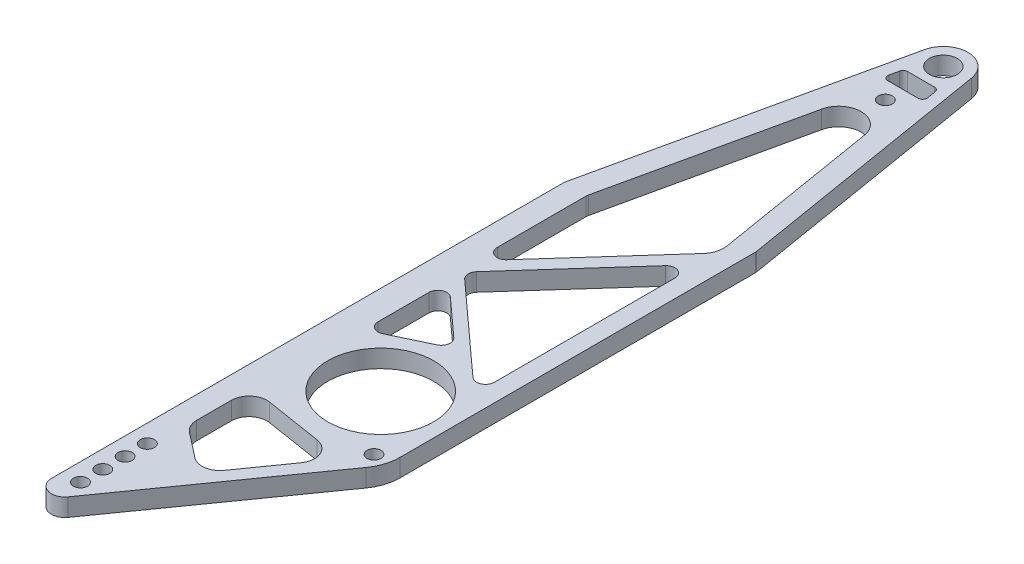
SolidWorks part; units mm, degrees
material "6061-T6 (SS)"
ref_plane "X-Y Datum" through (0, 0, 0) normal (0, 0, 1) x (1, 0, 0)
ref_plane "X-Z Datum" through (0, 0, 0) normal (0, 1, 0) x (1, 0, 0)
ref_plane "Y-Z Datum" through (0, 0, 0) normal (1, 0, 0) x (0, 0, -1)
other "Graphic1" [suppressed]
other "Graphic (Closed) -1" [suppressed]
sketch "Sketch1" plane through (0, 0, 0) normal (0, 1, 0) x (1, 0, 0)
  line L0 (25.4, -82.7357) -> (25.4, -202.7088)
  line L2 (-25.4, -229.1053) -> (-25.4, -131.2787)
  line L6 (25.4, -160.2465) -> (-25.4, -160.2465) construction
  line L28 (22.225, -208.2081) -> (-19.685, -232.4048)
  line L29 (0, 0) -> (41.91, 0) construction
  line L30 (41.91, 0) -> (0, -160.2465) construction
  line L31 (0, -160.2465) -> (0, 0) construction
  line L32 (-20.32, -219.075) -> (-20.32, -212.725) construction
  line L33 (25.2486, -81.3572) -> (6.8184, 1.5163)
  line L34 (-25.4, -131.2787) -> (-6.9178, 0.9668)
  circle A0 centre (0, 0) radius 3.9688
  circle A2 centre (0, -160.2465) radius 15.0813
  circle A6 centre (-20.32, -225.425) radius 2
  circle A7 centre (-20.32, -219.075) radius 2
  circle A8 centre (-20.32, -212.725) radius 2
  circle A9 centre (-20.32, -206.375) radius 2
  arc A10 (6.8184, 1.5163) -> (-6.9178, 0.9668) centre (0, 0) ccw
  circle A41 centre (0, -16.51) radius 2
  arc A42 (-25.4, -229.1053) -> (-19.685, -232.4048) centre (-21.59, -229.1053) ccw
  arc A43 (25.4, -202.7088) -> (22.225, -208.2081) centre (19.05, -202.7088) cw
  circle A45 centre (21.59, -82.0382) radius 2 construction
  arc A46 (25.2486, -81.3572) -> (25.4, -82.7357) centre (19.05, -82.7357) cw
  point P21 (-20.32, -215.9)
  point P30 (25.4, -206.375)
  point P51 (25.4, -82.0382)
  dimension "D1" = 7.9375
  dimension "D4" = 30.1625
  dimension "D8" = 4
  dimension "D6" = 6.985
  dimension "D65" = 4
  dimension "D18" = 3.81
  dimension "D20" = 6.35
  dimension "D32" = 4
  dimension "D34" = 6.35
  dimension "D9" = 5.08
  dimension "D11" = 6.35
  dimension "D12" = 6.35
  dimension "D13" = 6.35
  dimension "D5" = 50.8
  dimension "D66" = 16.51
  dimension "D2" = 41.91
  dimension "D3" = 165.6363
  dimension "D7" = 215.9
  dimension "D10" = 120
  dimension "D19" = 206.375
  dimension "D23" = 187.956
  dimension "D33" = 3.81
extrude "Boss-Extrude1" [suppressed] add sketch "Sketch1" against normal blind 6.35
sketch "Sketch9" [suppressed] plane through (0, 0, 0) normal (0, 1, 0) x (1, 0, 0)
  line L0 (0, 0) -> (0, -162.7876)
  line L1 (0, -162.7876) -> (41.91, 0)
  line L2 (41.91, 0) -> (0, 0)
  line L3 (0, 0) -> (39.3048, -10.1191) construction
  dimension "D1" = 168.096
  dimension "D2" = 0
  dimension "D3" = 41.91
  dimension "D4" = 40.5865
  dimension "D5" = 75.563
  dimension "D6" = 162.7876
sketch "Sketch4" [suppressed] plane through (0, 0, 0) normal (0, 1, 0) x (1, 0, 0)
  line L0 (0, -34.29) -> (0, 0)
  line L1 (0, 0) -> (152.4, 0)
  line L2 (152.4, 0) -> (0, -34.29)
  line L3 (0, 0) -> (7.3435, -32.6377) construction
  dimension "D1" = 12.68
  dimension "D2" = 156.21
  dimension "D3" = 34.29
  dimension "D4" = 152.4
  dimension "D5" = 33.4537
sketch "Sketch10" [suppressed] plane through (-25.4, 0, 0) normal (-1, 0, 0) x (0, 0, 1)
  line L0 (197.3553, 0) -> (197.3553, -6.35)
  line L1 (131.2787, 0) -> (229.1053, 0) construction
  line L2 (131.2787, -6.35) -> (229.1053, -6.35) construction
  line L5 (229.1053, -6.35) -> (229.1053, 0) construction
  dimension "D1" = 31.75
split line "Split Line1" [suppressed]
other "Graphic2" [suppressed]
other "Graphic (Closed) -2" [suppressed]
sketch "Sketch11" plane through (0, 0, 0) normal (0, 1, 0) x (1, 0, 0)
  line L2 (19.05, -173.7588) -> (19.05, -72.5986)
  line L3 (16.7146, -181.0981) -> (-18.4806, -230.8018)
  line L4 (0, 0) -> (41.91, 0) construction
  line L7 (-20.32, -219.075) -> (-20.32, -212.725) construction
  line L8 (19.016, -72.1842) -> (6.8914, 1.1395)
  line L10 (11.9403, -80.3341) -> (-14.464, -109.8371)
  line L12 (13.4735, -75.0634) -> (5.7192, -28.1694)
  line L14 (13.97, -141.8125) -> (13.97, -90.4261)
  line L15 (9.5373, -88.7321) -> (-15.8435, -117.0916)
  line L16 (-15.6576, -120.6667) -> (9.7233, -143.6937)
  line L18 (-13.2793, -127.1113) -> (-2.8095, -136.6101)
  line L23 (-25.4, -228.6) -> (-25.4, -177.8)
  line L24 (19.05, -72.39) -> (13.97, -78.0662) construction
  line L25 (6.2822, -189.2382) -> (-2.7798, -202.0357)
  line L27 (-17.526, -128.9925) -> (-17.526, -143.4613)
  line L30 (3.8345, -6.35) -> (-3.8345, -6.35)
  line L31 (-5.0746, -7.3459) -> (-5.636, -9.8859)
  line L32 (-4.3959, -11.43) -> (4.2545, -11.43)
  line L33 (5.5075, -9.9528) -> (5.0875, -7.4128)
  line L36 (-3.427, -140.7859) -> (-13.8968, -145.7559)
  line L37 (2.9318, -181.2851) -> (-13.1745, -178.7315)
  line L39 (-19.05, -193.6134) -> (-19.05, -183.7489)
  line L40 (-10.0472, -203.1078) -> (-17.0916, -197.6212)
  line L41 (-25.4, -177.8) -> (-25.4, -82.8274)
  line L42 (-25.3401, -82.2792) -> (-6.8204, 1.5075)
  line L43 (-6.8024, -27.8333) -> (-18.8369, -82.2792)
  line L44 (-18.8967, -82.8274) -> (-18.8967, -108.1432)
  circle A0 centre (0, 0) radius 3.9687
  circle A1 centre (0, -160.2465) radius 15.0813
  circle A2 centre (-20.32, -225.425) radius 2
  circle A3 centre (-20.32, -219.075) radius 2
  circle A4 centre (-20.32, -212.725) radius 2
  circle A5 centre (-20.32, -206.375) radius 2
  arc A6 (6.8914, 1.1395) -> (-6.8204, 1.5075) centre (0, 0) ccw
  circle A7 centre (0, -16.51) radius 2
  arc A8 (-25.4, -228.6) -> (-18.4806, -230.8018) centre (-21.59, -228.6) ccw
  arc A16 (-6.8024, -27.8333) -> (5.7192, -28.1694) centre (-0.574, -29.21) cw
  arc A17 (-5.636, -9.8859) -> (-4.3959, -11.43) centre (-4.3959, -10.16) ccw
  arc A18 (-5.0746, -7.3459) -> (-3.8345, -6.35) centre (-3.8345, -7.62) cw
  arc A19 (3.8345, -6.35) -> (5.0875, -7.4128) centre (3.8345, -7.62) cw
  arc A20 (5.5075, -9.9528) -> (4.2545, -11.43) centre (4.2545, -10.16) cw
  arc A21 (2.9318, -181.2851) -> (6.2822, -189.2382) centre (2.1363, -186.3025) cw
  arc A22 (-19.05, -183.7489) -> (-13.1745, -178.7315) centre (-13.97, -183.7489) cw
  arc A23 (-19.05, -193.6134) -> (-17.0916, -197.6212) centre (-13.97, -193.6134) ccw
  arc A24 (-10.0472, -203.1078) -> (-2.7798, -202.0357) centre (-6.9257, -199.1) ccw
  arc A26 (11.9403, -80.3341) -> (13.4735, -75.0634) centre (7.2085, -76.0993) ccw
  arc A27 (-17.526, -143.4613) -> (-13.8968, -145.7559) centre (-14.986, -143.4613) ccw
  arc A28 (-17.526, -128.9925) -> (-13.2793, -127.1113) centre (-14.986, -128.9925) cw
  arc A29 (-2.8095, -136.6101) -> (-3.427, -140.7859) centre (-4.5162, -138.4913) cw
  arc A30 (-15.8435, -117.0916) -> (-15.6576, -120.6667) centre (-13.9509, -118.7855) ccw
  arc A31 (9.7233, -143.6937) -> (13.97, -141.8125) centre (11.43, -141.8125) ccw
  arc A32 (9.5373, -88.7321) -> (13.97, -90.4261) centre (11.43, -90.4261) cw
  arc A33 (19.016, -72.1842) -> (19.05, -72.5986) centre (16.51, -72.5986) cw
  arc A35 (19.05, -173.7588) -> (16.7146, -181.0981) centre (6.35, -173.7588) cw
  circle A36 centre (14.605, -176.7565) radius 2
  arc A37 (-25.4, -82.8274) -> (-25.3401, -82.2792) centre (-22.86, -82.8274) cw
  arc A38 (-18.8967, -108.1432) -> (-14.464, -109.8371) centre (-16.3567, -108.1432) ccw
  arc A39 (-18.8369, -82.2792) -> (-18.8967, -82.8274) centre (-16.3567, -82.8274) ccw
  point P16 (-20.32, -215.9)
  point P60 (0, -6.35)
  point P66 (-19.05, -177.8)
  point P71 (-5.8525, -206.375)
  point P82 (-17.526, -123.2585)
  point P85 (0, -139.1591)
  point P88 (-17.526, -118.9715)
  point P91 (13.97, -147.5465)
  point P94 (13.97, -83.7792)
  point P100 (-25.4, -82.55)
  point P103 (19.05, -177.8)
  dimension "D1" = 7.9375
  dimension "D2" = 30.1625
  dimension "D3" = 4
  dimension "D9" = 6.985
  dimension "D10" = 4
  dimension "D16" = 3.81
  dimension "D17" = 50.8
  dimension "D19" = 6.35
  dimension "D20" = 19.05
  dimension "D26" = 144.698
  dimension "D27" = 6.35
  dimension "D28" = 12.7
  dimension "D30" = 3.81
  dimension "D35" = 1.27
  dimension "D38" = 5.08
  dimension "D39" = 2.54
  dimension "D40" = 2.54
  dimension "D41" = 2.54
  dimension "D42" = 6.35
  dimension "D43" = 12.7
  dimension "D44" = 4
  dimension "D49" = 2.54
  dimension "D50" = 2.54
  dimension "D4" = 5.08
  dimension "D5" = 6.35
  dimension "D6" = 6.35
  dimension "D7" = 6.35
  dimension "D8" = 228.6
  dimension "D11" = 16.51
  dimension "D12" = 41.91
  dimension "D13" = 160.2465
  dimension "D14" = 215.9
  dimension "D15" = 21.59
  dimension "D18" = 17.526
  dimension "D21" = 72.39
  dimension "D22" = 5.08
  dimension "D23" = 3.81
  dimension "D24" = 41.275
  dimension "D25" = 12.7
  dimension "D29" = 3.175
  dimension "D31" = 5.08
  dimension "D32" = 6.35
  dimension "D33" = 3.175
  dimension "D34" = 19.05
  dimension "D36" = 20.32
  dimension "D37" = 8.89
  dimension "D45" = 14.605
  dimension "D46" = 16.51
  dimension "D47" = 26.056
  dimension "D48" = 95.25
extrude "Boss-Extrude2" add sketch "Sketch11" against normal blind 5.08
sketch "Sketch13" plane through (-25.4, 0, 0) normal (-1, 0, 0) x (0, 0, 1)
  line L0 (196.85, 0) -> (196.85, -5.08)
  line L1 (82.8274, 0) -> (228.6, 0) construction
  line L2 (82.8274, -5.08) -> (228.6, -5.08) construction
  line L3 (228.6, -5.08) -> (228.6, 0) construction
  dimension "D1" = 31.75
split line "Split Line3"
equation "\"toePadMount\"=0.25"
equation "\"D11@Sketch1\"=\"toePadMount\""
equation "\"D12@Sketch1\"=\"toePadMount\""
equation "\"D13@Sketch1\"=\"toePadMount\""
